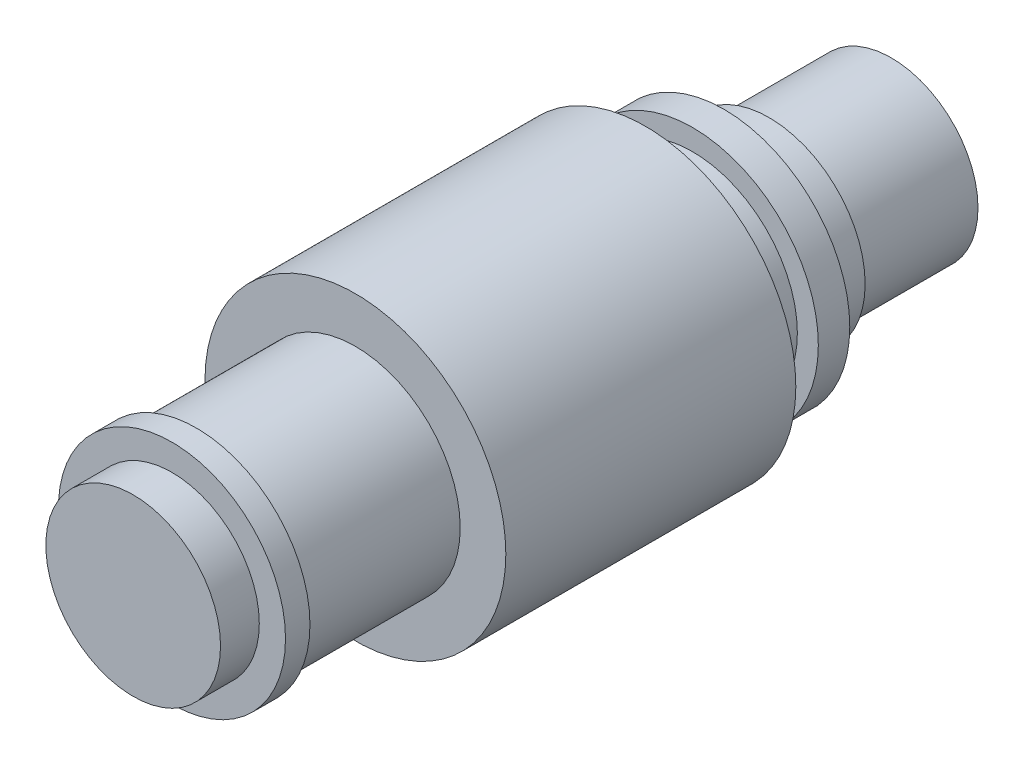
SolidWorks part; units mm, degrees
material "AISI 4130 Steel, annealed at 865C"
ref_plane "X-Y Datum" through (0, 0, 0) normal (0, 0, 1) x (1, 0, 0)
ref_plane "X-Z Datum" through (0, 0, 0) normal (0, 1, 0) x (1, 0, 0)
ref_plane "Y-Z Datum" through (0, 0, 0) normal (1, 0, 0) x (0, 0, -1)
sketch "Sketch3" plane through (0, 0, 0) normal (1, 0, 0) x (0, 0, -1)
  line L0 (0, 0) -> (217, 0)
  line L2 (182, 27.5) -> (169.1, 27.5)
  line L3 (169.1, 27.5) -> (169.1, 36)
  line L4 (169.1, 36) -> (160.1, 36)
  line L5 (160.1, 36) -> (160.1, 30)
  line L6 (160.1, 30) -> (18.1, 30)
  line L7 (18.1, 30) -> (18.1, 32.5)
  line L8 (18.1, 32.5) -> (11.1, 32.5)
  line L9 (11.1, 32.5) -> (11.1, 25)
  line L10 (11.1, 25) -> (0, 25)
  line L11 (0, 25) -> (0, 0)
  line L12 (182, 27.5) -> (182, 24.8)
  line L13 (182, 24.8) -> (217, 24.8)
  line L14 (217, 24.8) -> (217, 0)
  dimension "D1" = 25
  dimension "D2" = 32.5
  dimension "D3" = 27.5
  dimension "D4" = 36
  dimension "D5" = 9
  dimension "D6" = 7
  dimension "D7" = 142
  dimension "D8" = 18.1
  dimension "D9" = 30
  dimension "D10" = 21.9
  dimension "D11" = 35
  dimension "D12" = 24.8
revolve "Revolve1" add sketch "Sketch3" angle 360 about L0
sketch "Sketch4" plane through (0, 0, -105.1) normal (0, 0, 1) x (1, 0, 0)
  circle A0 centre (0, 0) radius 43.0575
extrude "Boss-Extrude1" add sketch "Sketch4" along normal mid plane 83
